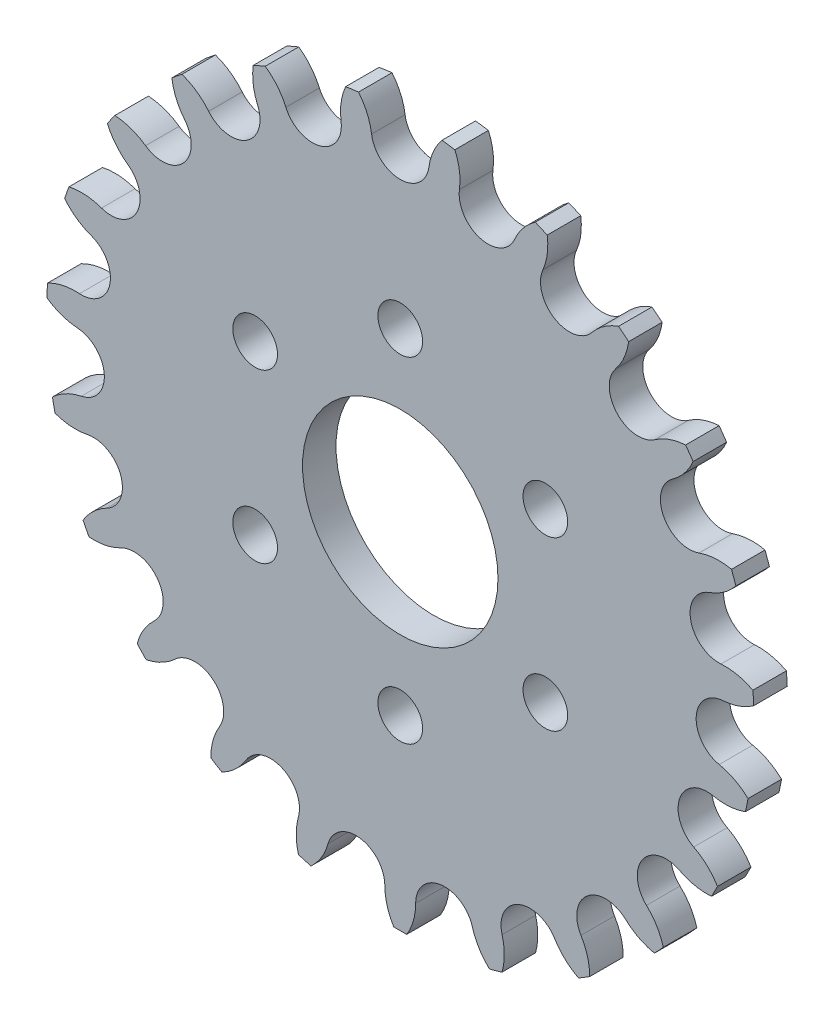
SolidWorks part; units mm, degrees
material "AISI 1020"
ref_plane "Спереди" through (0, 0, 0) normal (0, 0, 1) x (1, 0, 0)
ref_plane "Сверху" through (0, 0, 0) normal (0, 1, 0) x (1, 0, 0)
ref_plane "Справа" through (0, 0, 0) normal (1, 0, 0) x (0, 0, -1)
sketch "Эскиз1" plane through (0, 0, 0) normal (0, 0, 1) x (1, 0, 0)
  line L0 (0, 0) -> (0, 85) construction
  line L1 (0, 85) -> (15.8056, 83.5176) construction
  line L2 (15.8056, 83.5176) -> (0, 0) construction
  line L3 (15.8056, 83.5176) -> (49.3989, 83.5176)
  line L4 (0, 0) -> (0, 58.2925)
  line L5 (0, 58.2925) -> (15.7271, 56.1309)
  line L6 (15.7271, 56.1309) -> (0, 0)
  circle A0 centre (0, 0) radius 85 construction
  circle A1 centre (0, 58.2925) radius 5.08
  circle A2 centre (15.7271, 56.1309) radius 5.08
  dimension "D1" = 170
  dimension "D6" = 10.16
  dimension "D2" = 15.875
  dimension "D3" = 10.716
  dimension "D4" = 33.5932
  dimension "D5" = 15.652
sketch "Эскиз2" plane through (0, 0, 0) normal (0, 0, 1) x (1, 0, 0)
  line L0 (0, 0) -> (0, 53.1125)
  line L1 (0, 0) -> (14.3296, 51.143)
  line L4 (15.7271, 56.1309) -> (0, 0) construction
  arc A0 (10.5954, 56.8362) -> (9.7836, 62.6128) centre (0, 58.2925) ccw
  arc A1 (0, 63.3725) -> (17.0977, 61.0225) centre (0, 0) cw construction
  circle A2 centre (0, 58.2925) radius 5.08 construction
  circle A3 centre (15.7271, 56.1309) radius 5.08 construction
  circle A4 centre (0, 0) radius 85 construction
  circle A5 centre (0, 58.2925) radius 5.18
  arc A6 (0, 53.1125) -> (5.1318, 57.5872) centre (0, 58.2925) ccw
  arc A7 (7.4719, 62.9305) -> (5.1318, 57.5872) centre (15.7271, 56.1309) ccw
  circle A8 centre (15.7271, 56.1309) radius 5.18
  arc A9 (10.5954, 56.8362) -> (14.3296, 51.143) centre (15.7271, 56.1309) ccw
  arc A10 (7.4719, 62.9305) -> (9.7836, 62.6128) centre (0, 0) cw
  dimension "D1" = 0.1
  dimension "D2" = 0.1
extrude "Бобышка-Вытянуть1" add sketch "Эскиз2" along normal blind 6
pattern_circular "Круговой массив1" count 23 over 360 about axis through (0, 0, 0) along (0, 0, 1) of "Бобышка-Вытянуть1"
sketch "Эскиз3" plane through (0, 0, 6) normal (0, 0, 1) x (1, 0, 0)
  line L0 (0, 0) -> (0, 30) construction
  line L1 (0, 0) -> (25.9808, 15) construction
  circle A0 centre (0, 0) radius 17.5
  circle A1 centre (0, 0) radius 30 construction
  circle A2 centre (0, 30) radius 4
  circle A3 centre (25.9808, 15) radius 4
  circle A4 centre (25.9808, -15) radius 4
  circle A5 centre (0, -30) radius 4
  circle A6 centre (-25.9808, -15) radius 4
  circle A7 centre (-25.9808, 15) radius 4
  dimension "D1" = 35
  dimension "D2" = 60
  dimension "D3" = 8
  dimension "D5" = 60
  dimension "D6" = 30
  dimension "D4" = 6
extrude "Вырез-Вытянуть1" cut sketch "Эскиз3" against normal through all
equation "\"D4@Эскиз1\"=360/\"D3@Эскиз1\""
equation "\"D5@Эскиз1\"=360/23"
